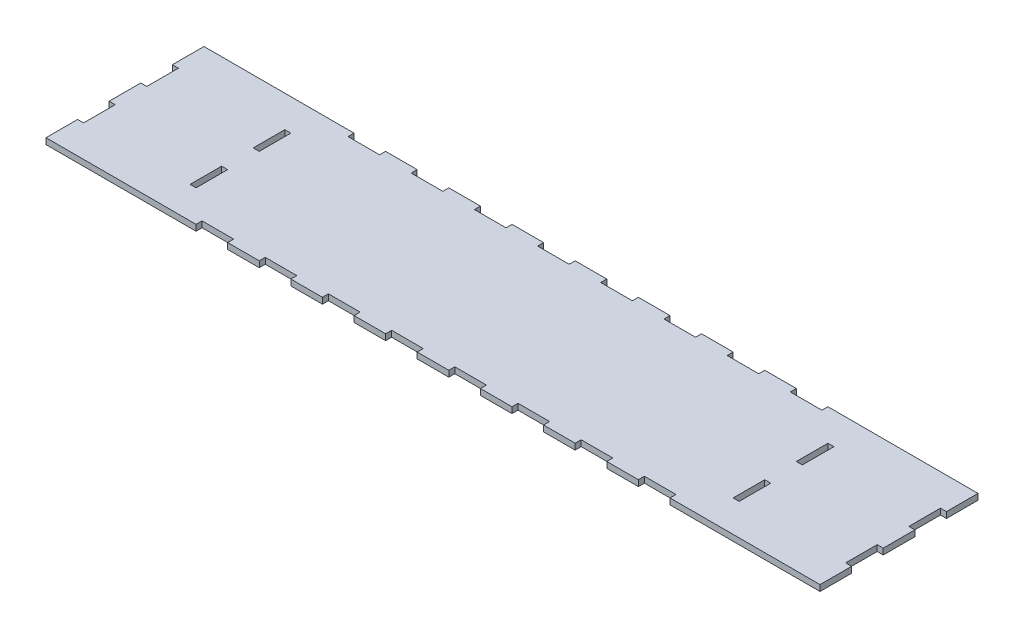
SolidWorks part; units mm, degrees
material "1060 Alloy"
ref_plane "Front Plane" through (0, 0, 0) normal (0, 0, 1) x (1, 0, 0)
ref_plane "Top Plane" through (0, 0, 0) normal (0, 1, 0) x (1, 0, 0)
ref_plane "Right Plane" through (0, 0, 0) normal (1, 0, 0) x (0, 0, -1)
sketch "Sketch1" plane through (0, 0, 0) normal (0, 1, 0) x (1, 0, 0)
  line L0 (4.826, 101.6) -> (4.826, 127) construction
  line L1 (0, 0) -> (622.3, 0)
  line L2 (0, 0) -> (0, 127)
  line L3 (0, 127) -> (622.3, 127)
  line L4 (622.3, 0) -> (622.3, 127)
  line L5 (0, 101.6) -> (4.826, 101.6)
  line L6 (0, 101.6) -> (0, 76.2)
  line L7 (0, 76.2) -> (4.826, 76.2)
  line L8 (4.826, 101.6) -> (4.826, 76.2)
  line L9 (0, 50.8) -> (4.826, 50.8)
  line L10 (0, 50.8) -> (0, 25.4)
  line L11 (0, 25.4) -> (4.826, 25.4)
  line L12 (4.826, 50.8) -> (4.826, 25.4)
  line L13 (90.424, 101.6) -> (95.25, 101.6)
  line L14 (90.424, 101.6) -> (90.424, 76.2)
  line L15 (90.424, 76.2) -> (95.25, 76.2)
  line L16 (95.25, 101.6) -> (95.25, 76.2)
  line L17 (90.424, 50.8) -> (95.25, 50.8)
  line L18 (90.424, 50.8) -> (90.424, 25.4)
  line L19 (90.424, 25.4) -> (95.25, 25.4)
  line L20 (95.25, 50.8) -> (95.25, 25.4)
  line L21 (527.05, 101.6) -> (531.876, 101.6)
  line L22 (527.05, 101.6) -> (527.05, 76.2)
  line L23 (527.05, 76.2) -> (531.876, 76.2)
  line L24 (531.876, 101.6) -> (531.876, 76.2)
  line L25 (527.05, 50.8) -> (531.876, 50.8)
  line L26 (527.05, 50.8) -> (527.05, 25.4)
  line L27 (527.05, 25.4) -> (531.876, 25.4)
  line L28 (531.876, 50.8) -> (531.876, 25.4)
  line L29 (617.474, 101.6) -> (622.3, 101.6)
  line L30 (617.474, 101.6) -> (617.474, 76.2)
  line L31 (617.474, 76.2) -> (622.3, 76.2)
  line L32 (622.3, 101.6) -> (622.3, 76.2)
  line L33 (617.474, 50.8) -> (622.3, 50.8)
  line L34 (617.474, 50.8) -> (617.474, 25.4)
  line L35 (617.474, 25.4) -> (622.3, 25.4)
  line L36 (622.3, 50.8) -> (622.3, 25.4)
  line L37 (4.826, 76.2) -> (4.826, 50.8) construction
  line L38 (4.826, 25.4) -> (4.826, 0) construction
  dimension "D1" = 622.3
  dimension "D2" = 127
  dimension "D3" = 4.826
  dimension "D4" = 95.25
  dimension "D5" = 95.25
extrude "Boss-Extrude1" add sketch "Sketch1" along normal blind 4.826 contours L35 L34 L33 L4 L31 L30 L29 L3 L2 L5 L8 L7 L9 L12 L11 L1 L13 L16 L15 L14 L17 L20 L19 L18 L21 L24 L23 L22 L25 L28 L27 L26
sketch "Sketch2" plane through (0, 4.826, 0) normal (0, 1, 0) x (1, 0, 0)
  line L0 (527.05, 127) -> (527.05, 97.1487) construction
  line L2 (622.3, 101.6) -> (622.3, 127) construction
  line L3 (95.25, -44.5807) -> (95.25, 215.2875) construction
  line L4 (0, 101.6) -> (0, 127) construction
  line L5 (0, 127) -> (622.3, 127) construction
  line L6 (120.65, 127) -> (146.05, 127)
  line L7 (120.65, 127) -> (120.65, 122.174)
  line L8 (120.65, 122.174) -> (146.05, 122.174)
  line L9 (146.05, 127) -> (146.05, 122.174)
  line L10 (196.85, 127) -> (196.85, 122.174)
  line L11 (171.45, 122.174) -> (196.85, 122.174)
  line L12 (171.45, 127) -> (196.85, 127)
  line L13 (171.45, 127) -> (171.45, 122.174)
  line L14 (247.65, 127) -> (247.65, 122.174)
  line L15 (222.25, 122.174) -> (247.65, 122.174)
  line L16 (222.25, 127) -> (247.65, 127)
  line L17 (222.25, 127) -> (222.25, 122.174)
  line L18 (298.45, 127) -> (298.45, 122.174)
  line L19 (273.05, 122.174) -> (298.45, 122.174)
  line L20 (273.05, 127) -> (298.45, 127)
  line L21 (273.05, 127) -> (273.05, 122.174)
  line L22 (349.25, 127) -> (349.25, 122.174)
  line L23 (323.85, 122.174) -> (349.25, 122.174)
  line L24 (323.85, 127) -> (349.25, 127)
  line L25 (323.85, 127) -> (323.85, 122.174)
  line L26 (400.05, 127) -> (400.05, 122.174)
  line L27 (374.65, 122.174) -> (400.05, 122.174)
  line L28 (374.65, 127) -> (400.05, 127)
  line L29 (374.65, 127) -> (374.65, 122.174)
  line L30 (450.85, 127) -> (450.85, 122.174)
  line L31 (425.45, 122.174) -> (450.85, 122.174)
  line L32 (425.45, 127) -> (450.85, 127)
  line L33 (425.45, 127) -> (425.45, 122.174)
  line L34 (501.65, 127) -> (501.65, 122.174)
  line L35 (476.25, 122.174) -> (501.65, 122.174)
  line L36 (476.25, 127) -> (501.65, 127)
  line L37 (476.25, 127) -> (476.25, 122.174)
  line L38 (81.7987, 63.5) -> (183.2637, 63.5) construction
  line L39 (0, 0) -> (622.3, 0) construction
  line L40 (476.25, 0) -> (476.25, 4.826)
  line L41 (476.25, 0) -> (501.65, 0)
  line L42 (476.25, 4.826) -> (501.65, 4.826)
  line L43 (501.65, 0) -> (501.65, 4.826)
  line L44 (425.45, 0) -> (425.45, 4.826)
  line L45 (425.45, 0) -> (450.85, 0)
  line L46 (425.45, 4.826) -> (450.85, 4.826)
  line L47 (450.85, 0) -> (450.85, 4.826)
  line L48 (374.65, 0) -> (374.65, 4.826)
  line L49 (374.65, 0) -> (400.05, 0)
  line L50 (374.65, 4.826) -> (400.05, 4.826)
  line L51 (400.05, 0) -> (400.05, 4.826)
  line L52 (323.85, 0) -> (323.85, 4.826)
  line L53 (323.85, 0) -> (349.25, 0)
  line L54 (323.85, 4.826) -> (349.25, 4.826)
  line L55 (349.25, 0) -> (349.25, 4.826)
  line L56 (146.05, 0) -> (146.05, 4.826)
  line L57 (120.65, 4.826) -> (146.05, 4.826)
  line L58 (120.65, 0) -> (120.65, 4.826)
  line L59 (120.65, 0) -> (146.05, 0)
  line L60 (171.45, 0) -> (171.45, 4.826)
  line L61 (171.45, 0) -> (196.85, 0)
  line L62 (171.45, 4.826) -> (196.85, 4.826)
  line L63 (196.85, 0) -> (196.85, 4.826)
  line L64 (222.25, 0) -> (222.25, 4.826)
  line L65 (222.25, 0) -> (247.65, 0)
  line L66 (222.25, 4.826) -> (247.65, 4.826)
  line L67 (247.65, 0) -> (247.65, 4.826)
  line L68 (273.05, 0) -> (273.05, 4.826)
  line L69 (273.05, 0) -> (298.45, 0)
  line L70 (273.05, 4.826) -> (298.45, 4.826)
  line L71 (298.45, 0) -> (298.45, 4.826)
  dimension "D1" = 95.25
  dimension "D2" = 95.25
  dimension "D3" = 25.4
  dimension "D4" = 25.4
  dimension "D5" = 4.826
  dimension "D6" = 8
extrude "Cut-Extrude1" cut sketch "Sketch2" against normal through all
equation "\"sheet width\"= .19"
equation "\"width\"= 24.5"
equation "\"length\"= 34.5"
equation "\"standoff hole size\"= .5"
equation "\"ground clearence\"= 3"
equation "\"small drive pulley\"= 74.55mm"
equation "\"large drive pulley\"= 150.95mm"
equation "\"drive axle hole size\"= .5"
equation "\"front pulley clearence\"= 1"
equation "\"center support location\"= 19"
equation "\"inner to outer wall size\"= 3.75"
equation "\"D3@Sketch1\"=\"sheet width\""
equation "\"D4@Sketch1\"=\"inner to outer wall size\""
equation "\"D5@Sketch1\"=\"inner to outer wall size\""
equation "\"D1@Boss-Extrude1\"=\"sheet width\""
equation "\"D1@Sketch1\"=\"width\""
equation "\"D1@Sketch2\"=\"inner to outer wall size\""
equation "\"D2@Sketch2\"=\"inner to outer wall size\""
equation "\"D5@Sketch2\"=\"sheet width\""
